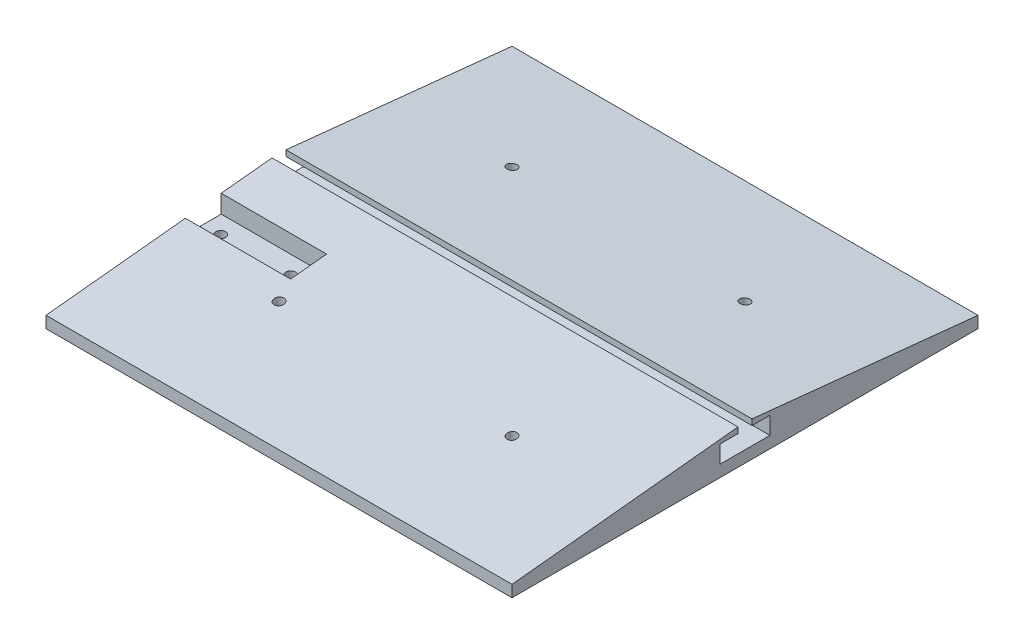
SolidWorks part; units mm, degrees
ref_plane "Front Plane" through (0, 0, 0) normal (0, 0, 1) x (1, 0, 0)
ref_plane "Top Plane" through (0, 0, 0) normal (0, 1, 0) x (1, 0, 0)
ref_plane "Right Plane" through (0, 0, 0) normal (1, 0, 0) x (0, 0, -1)
sketch "Sketch1" plane through (0, 0, 0) normal (0, 1, 0) x (1, 0, 0)
  line L1 (100, -100) -> (-100, -100)
  line L2 (100, -100) -> (100, 100)
  line L3 (100, 100) -> (-100, 100)
  line L4 (-100, -100) -> (-100, 100)
  line L5 (100, -100) -> (-100, 100) construction
  line L6 (100, 100) -> (-100, -100) construction
  point P0 (0, 0)
  dimension "D1" = 200
  dimension "D2" = 200
extrude "Boss-Extrude1" add sketch "Sketch1" along normal blind 5
sketch "Sketch9" plane through (100, 0, 0) normal (1, 0, 0) x (0, 0, -1)
  line L0 (-100, 5) -> (-3, 15)
  line L1 (-3, 15) -> (-3, 5)
  line L2 (-100, 5) -> (100, 5) construction
  line L3 (-3, 5) -> (-100, 5)
  line L4 (0, 0) -> (0, 15) construction
  line L5 (3, 5) -> (100, 5)
  line L6 (3, 15) -> (3, 5)
  line L7 (100, 5) -> (3, 15)
  dimension "D1" = 97
  dimension "D2" = 10
extrude "Boss-Extrude2" add sketch "Sketch9" against normal up to surface (200 mm away) up to face at (-100, 2.5, 0)
sketch "Sketch13" plane through (-100, 0, 0) normal (-1, 0, 0) x (0, 0, 1)
  line L0 (-3, 5) -> (3, 5) construction
  line L1 (-10.7, 12.5) -> (10.7, 12.5)
  line L2 (-10.7, 12.5) -> (-10.7, 5)
  line L3 (-10.7, 5) -> (10.7, 5)
  line L4 (10.7, 12.5) -> (10.7, 5)
  line L5 (0, 0) -> (0, 14.9801) construction
  dimension "D1" = 21.4
  dimension "D2" = 7.5
extrude "Cut-Extrude9" cut sketch "Sketch13" against normal up to next
sketch "Sketch17" plane through (0, 0, 0) normal (0, -1, 0) x (1, 0, 0)
  line L1 (50, -50) -> (-50, -50) construction
  line L2 (50, -50) -> (50, 50) construction
  line L3 (50, 50) -> (-50, 50) construction
  line L4 (-50, -50) -> (-50, 50) construction
  line L5 (50, -50) -> (-50, 50) construction
  line L6 (50, 50) -> (-50, -50) construction
  circle A0 centre (-50, 50) radius 2.1
  circle A1 centre (50, 50) radius 2.1
  circle A2 centre (50, -50) radius 2.1
  circle A3 centre (-50, -50) radius 2.1
  point P0 (0, 0)
  dimension "D2" = 4.2
  dimension "D1" = 100
  dimension "D3" = 2
  dimension "D4" = 2
sketch "Sketch18" plane through (0, 0, 0) normal (0, -1, 0) x (1, 0, 0)
  line L1 (50, -50) -> (-50, -50) construction
  line L2 (50, -50) -> (50, 50) construction
  line L3 (50, 50) -> (-50, 50) construction
  line L4 (-50, -50) -> (-50, 50) construction
  line L5 (50, -50) -> (-50, 50) construction
  line L6 (50, 50) -> (-50, -50) construction
  line L9 (-52.1362, 46.3) -> (-47.8638, 46.3)
  line L10 (-47.8638, 46.3) -> (-45.7276, 50)
  line L11 (-45.7276, 50) -> (-47.8638, 53.7)
  line L12 (-47.8638, 53.7) -> (-52.1362, 53.7)
  line L14 (47.8638, 46.3) -> (52.1362, 46.3)
  line L15 (52.1362, 46.3) -> (54.2724, 50)
  line L16 (54.2724, 50) -> (52.1362, 53.7)
  line L17 (52.1362, 53.7) -> (47.8638, 53.7)
  line L20 (47.8638, -53.7) -> (52.1362, -53.7)
  line L21 (52.1362, -53.7) -> (54.2724, -50)
  line L22 (54.2724, -50) -> (52.1362, -46.3)
  line L23 (52.1362, -46.3) -> (47.8638, -46.3)
  line L26 (-52.1362, -53.7) -> (-47.8638, -53.7)
  line L27 (-47.8638, -53.7) -> (-45.7276, -50)
  line L28 (-45.7276, -50) -> (-47.8638, -46.3)
  line L29 (-47.8638, -46.3) -> (-52.1362, -46.3)
  line L30 (-52.1362, 46.3) -> (-54.2724, 46.3)
  line L31 (-54.2724, 46.3) -> (-54.2724, 53.7)
  line L32 (-54.2724, 53.7) -> (-52.1362, 53.7)
  line L33 (-52.1362, -53.7) -> (-54.2724, -53.7)
  line L34 (-54.2724, -53.7) -> (-54.2724, -46.3)
  line L35 (-54.2724, -46.3) -> (-52.1362, -46.3)
  line L36 (47.8638, -53.7) -> (45.7276, -53.7)
  line L37 (45.7276, -53.7) -> (45.7276, -46.3)
  line L38 (45.7276, -46.3) -> (47.8638, -46.3)
  line L39 (47.8638, 46.3) -> (45.7276, 46.3)
  line L40 (45.7276, 46.3) -> (45.7276, 53.7)
  line L41 (45.7276, 53.7) -> (47.8638, 53.7)
  line L49 (-54.2724, 50) -> (-53.2043, 48.15) [skipped]
  line L50 (-52.1362, 53.7) -> (-53.2043, 51.85) [skipped]
  circle A0 centre (-50, 50) radius 3.7 construction
  circle A1 centre (50, 50) radius 3.7 construction
  circle A2 centre (50, -50) radius 3.7 construction
  circle A3 centre (-50, -50) radius 3.7 construction
  point P0 (0, 0)
  dimension "D1" = 100
  dimension "D2" = 7.4
  dimension "D3" = 2
  dimension "D4" = 2
extrude "Cut-Extrude14" cut sketch "Sketch18" against normal blind 3.6 from offset 2 offset against normal yes
extrude "Cut-Extrude15" cut sketch "Sketch17" against normal through all
move or copy body "Body-Move/Copy1" bodies to move or copy 110 parameters "D1"=0, "D2"=0, "D3"=0
sketch "Sketch19" plane through (-100, 0, 0) normal (-1, 0, 0) x (0, 0, 1)
  line L0 (3, 15) -> (100, 5) construction
  line L1 (24.8, 12.7526) -> (40.2, 12.7526)
  line L2 (24.8, 12.7526) -> (24.8, 5)
  line L3 (24.8, 5) -> (40.2, 5)
  line L4 (40.2, 12.7526) -> (40.2, 5)
  line L5 (10.7, 5) -> (-10.7, 5) construction
  line L6 (10.7, 12.5) -> (10.7, 5) construction
  dimension "D1" = 14.1
  dimension "D2" = 15.4
extrude "Cut-Extrude16" cut sketch "Sketch19" against normal blind 45.2
sketch "Sketch20" plane through (0, 5, 0) normal (0, 1, 0) x (1, 0, 0)
  line L0 (-100, -32.5) -> (-54.8, -32.5) construction
  line L1 (-100, -24.8) -> (-100, -40.2) construction
  line L2 (-54.8, -24.8) -> (-54.8, -40.2) construction
  circle A0 centre (-92.5, -32.5) radius 2.1
  circle A1 centre (-62.5, -32.5) radius 2.1
  dimension "D1" = 4.2
  dimension "D2" = 30
  dimension "D3" = 7.5
extrude "Cut-Extrude17" cut sketch "Sketch20" against normal blind 45
